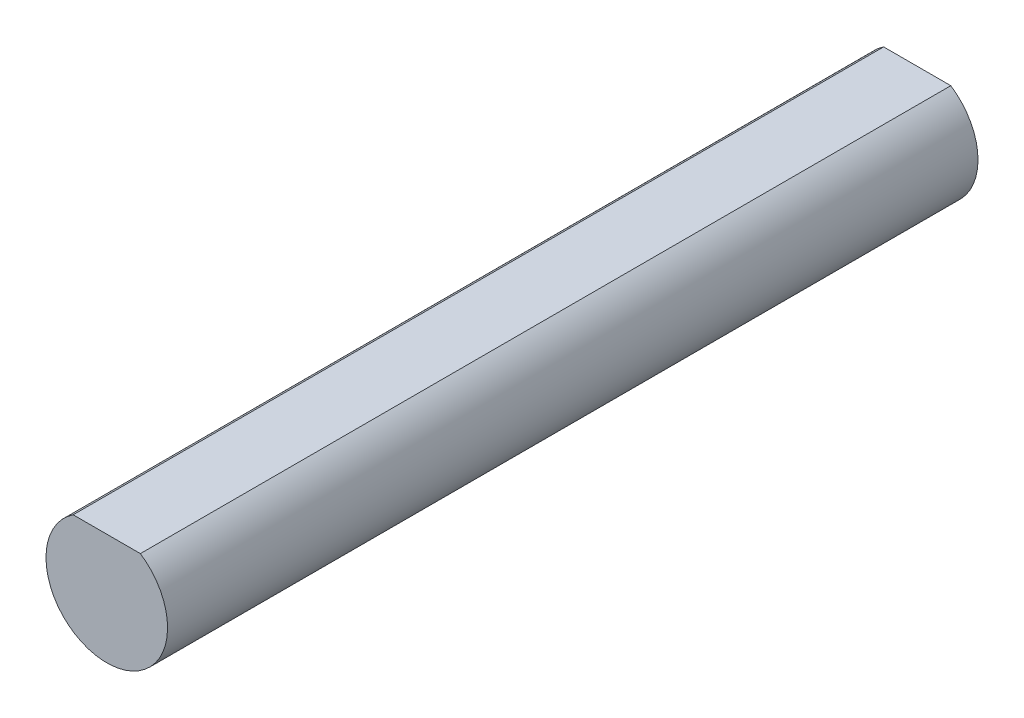
SolidWorks part; units mm, degrees
ref_plane "Front Plane" through (0, 0, 0) normal (0, 0, 1) x (1, 0, 0)
ref_plane "Top Plane" through (0, 0, 0) normal (0, 1, 0) x (1, 0, 0)
ref_plane "Right Plane" through (0, 0, 0) normal (1, 0, 0) x (0, 0, -1)
sketch "Sketch1" plane through (0, 0, 0) normal (0, 0, 1) x (1, 0, 0)
  line L0 (-1.6583, 2.5) -> (1.6583, 2.5)
  arc A0 (-1.6583, 2.5) -> (1.6583, 2.5) centre (0, 0) ccw
  dimension "D1" = 6
  dimension "D2" = 2.5
extrude "Boss-Extrude1" add sketch "Sketch1" along normal blind 40
